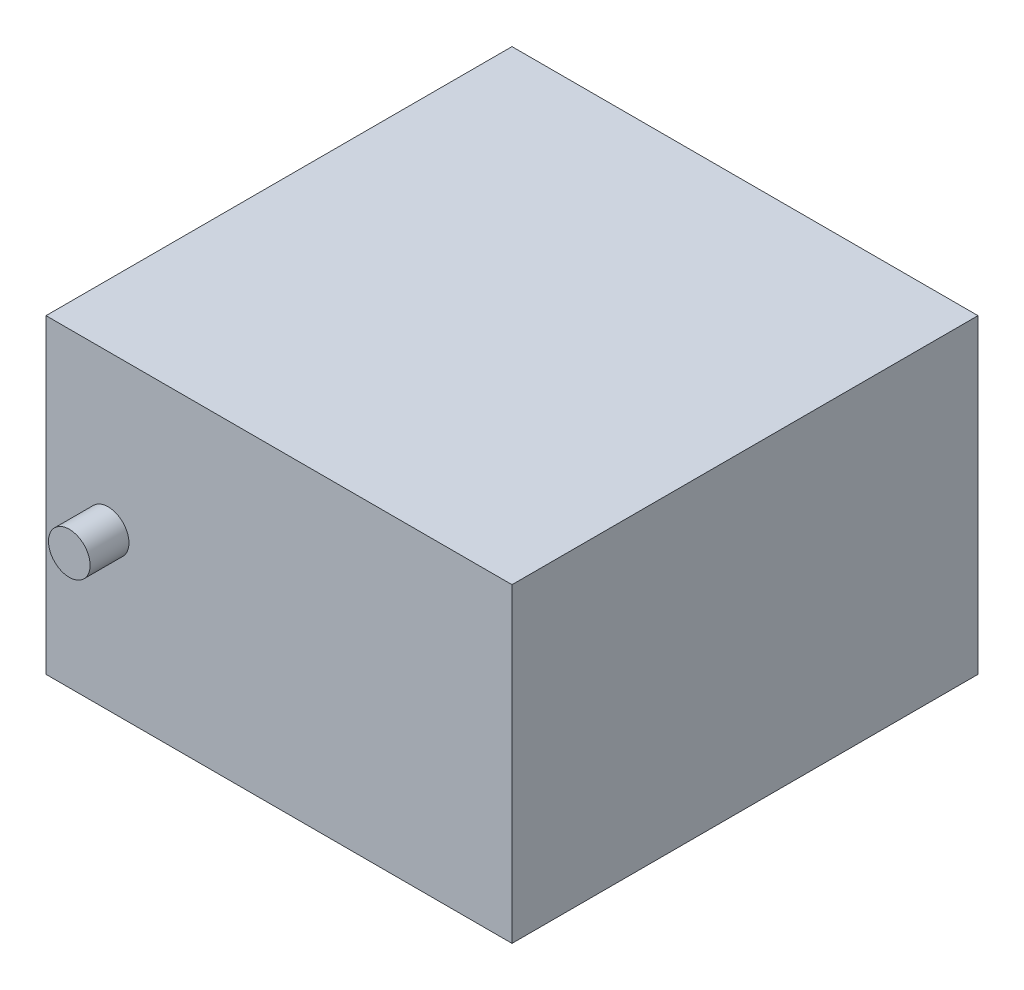
SolidWorks part; units mm, degrees
ref_plane "Front Plane" through (0, 0, 0) normal (0, 0, 1) x (1, 0, 0)
ref_plane "Top Plane" through (0, 0, 0) normal (0, 1, 0) x (1, 0, 0)
ref_plane "Right Plane" through (0, 0, 0) normal (1, 0, 0) x (0, 0, -1)
sketch "Sketch1" plane through (0, 0, 0) normal (0, 0, 1) x (1, 0, 0)
  line L1 (-32.3188, 20.8696) -> (7.6812, 20.8696)
  line L2 (-32.3188, 20.8696) -> (-32.3188, 0.8696)
  line L3 (-32.3188, 0.8696) -> (7.6812, 0.8696)
  line L4 (7.6812, 20.8696) -> (7.6812, 0.8696)
  dimension "D1" = 40
  dimension "D2" = 20
extrude "Boss-Extrude1" add sketch "Sketch1" along normal blind 40
sketch "Sketch2" plane through (0, 0, 40) normal (0, 0, 1) x (1, 0, 0)
  line L0 (7.6812, 20.8696) -> (-32.3188, 20.8696) construction
  line L2 (-32.3188, 20.8696) -> (-32.3188, 0.8696) construction
  circle A0 centre (-28.3188, 10.8696) radius 1.3408
  dimension "D1" = 10
  dimension "D2" = 4
extrude "Boss-Extrude2" add sketch "Sketch2" along normal blind 2.5
sketch "Sketch3" plane through (0, 0.8696, 0) normal (0, -1, 0) x (1, 0, 0)
  line L0 (7.6812, 40) -> (7.6812, 0) construction
  line L1 (-32.3188, 0) -> (7.6812, 0)
  line L2 (-32.3188, 0) -> (-32.3188, 10)
  line L3 (-32.3188, 10) -> (7.6812, 10)
  line L4 (7.6812, 0) -> (7.6812, 10)
  dimension "D1" = 10
extrude "Cut-Extrude1" cut sketch "Sketch3" against normal blind 20
sketch "Sketch5" plane through (0, 0.8696, 0) normal (0, -1, 0) x (1, 0, 0)
  line L0 (7.6812, 10) -> (-32.3188, 10) construction
  line L1 (7.6812, 40) -> (-2.3188, 40)
  line L2 (7.6812, 40) -> (7.6812, 10)
  line L3 (7.6812, 10) -> (-2.3188, 10)
  line L4 (-2.3188, 40) -> (-2.3188, 10)
  dimension "D1" = 10
extrude "Cut-Extrude4" cut sketch "Sketch5" against normal blind 20
